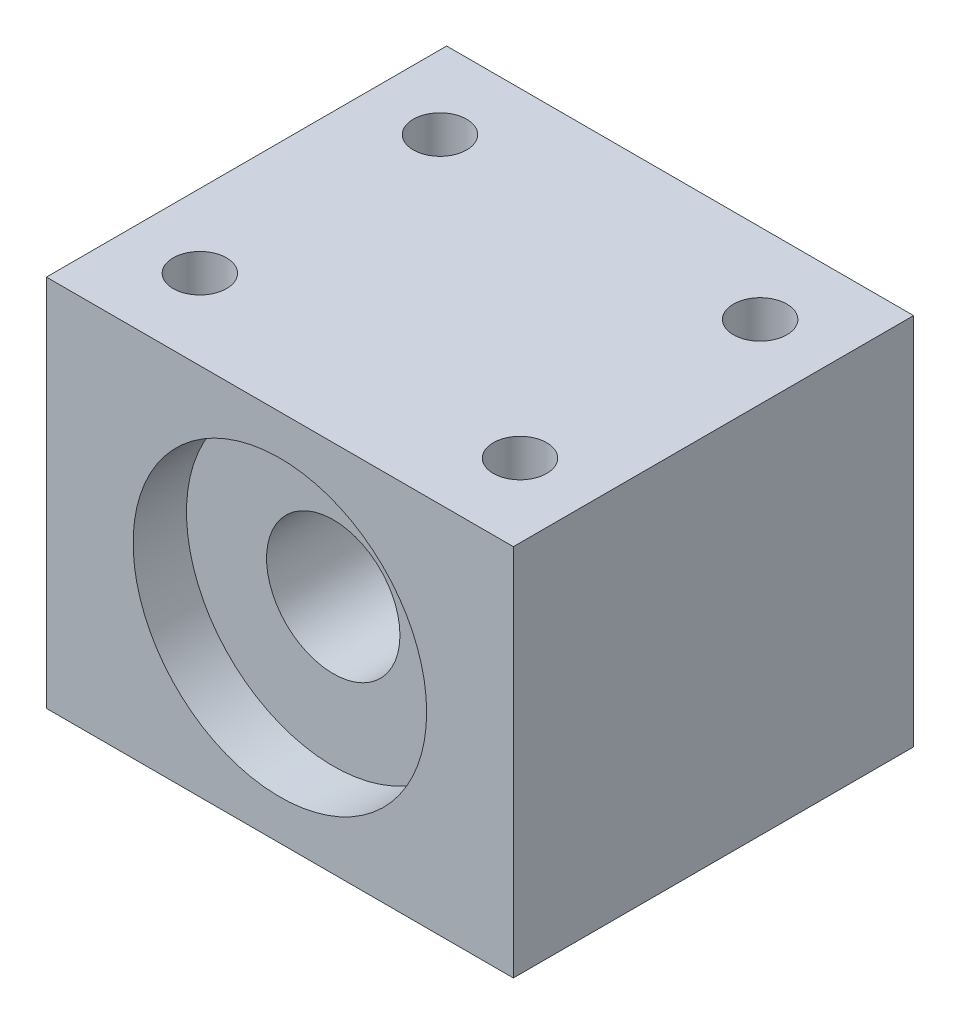
SolidWorks part; units mm, degrees
ref_plane "Alzado" through (0, 0, 0) normal (0, 0, 1) x (1, 0, 0)
ref_plane "Planta" through (0, 0, 0) normal (0, 1, 0) x (1, 0, 0)
ref_plane "Vista lateral" through (0, 0, 0) normal (1, 0, 0) x (0, 0, -1)
sketch "Sketch1" plane through (0, 0, 0) normal (0, 1, 0) x (1, 0, 0)
  line L0 (0, 15) -> (0, -15) construction
  line L1 (-17.5, -15) -> (17.5, -15)
  line L2 (-17.5, -15) -> (-17.5, 15)
  line L3 (-17.5, 15) -> (17.5, 15)
  line L4 (17.5, -15) -> (17.5, 15)
  line L5 (-17.5, 0) -> (17.5, 0) construction
  circle A0 centre (-12, 9) radius 2
  circle A1 centre (-12, -9) radius 2
  circle A2 centre (12, -9) radius 2
  circle A3 centre (12, 9) radius 2
  point P0 (0, 0)
  dimension "D7" = 4
  dimension "D1" = 35
  dimension "D2" = 30
  dimension "D3" = 5.5
  dimension "D4" = 17.5
  dimension "D5" = 15
  dimension "D6" = 6
extrude "Boss-Extrude1" add sketch "Sketch1" along normal blind 28
sketch "Sketch2" plane through (0, 0, 15) normal (0, 0, 1) x (1, 0, 0)
  line L0 (-17.5, 28) -> (-17.5, 0) construction
  line L1 (-17.5, 28) -> (17.5, 28) construction
  circle A0 centre (0, 14) radius 11
  point P2 (0.5975, 16.0236)
  dimension "D1" = 22
  dimension "D2" = 17.5
  dimension "D3" = 14
extrude "Cut-Extrude1" cut sketch "Sketch2" against normal blind 4
sketch "Sketch3" plane through (0, 0, 11) normal (0, 0, 1) x (1, 0, 0)
  circle A0 centre (0, 14) radius 5
  dimension "D1" = 10
extrude "Cut-Extrude2" cut sketch "Sketch3" against normal through all contours A0
